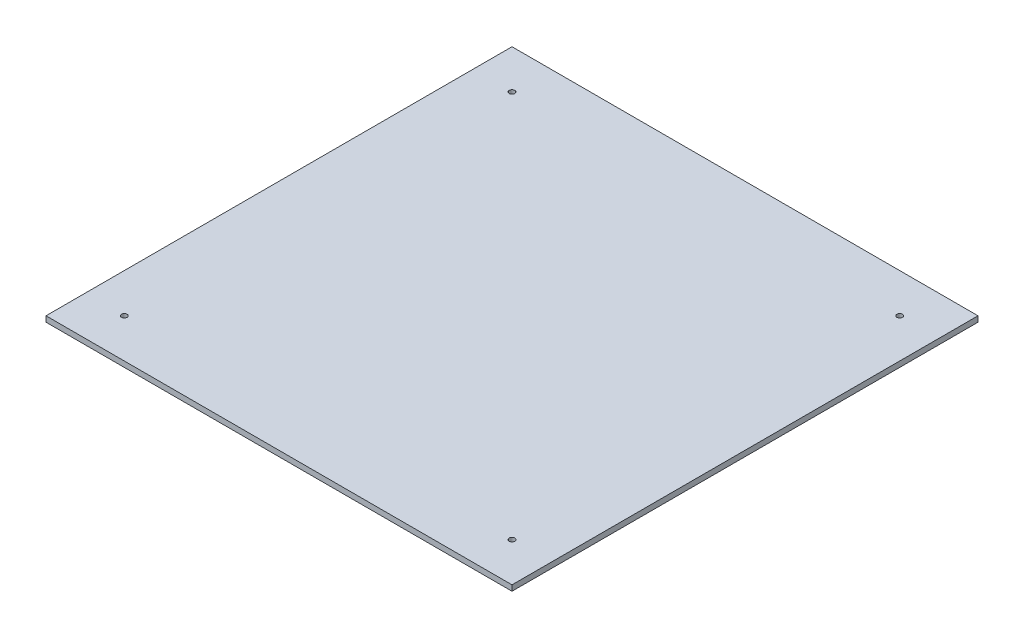
SolidWorks part; units mm, degrees
material "Balsa"
ref_plane "Plano frontal" through (0, 0, 0) normal (0, 0, 1) x (1, 0, 0)
ref_plane "Plano superior" through (0, 0, 0) normal (0, 1, 0) x (1, 0, 0)
ref_plane "Plano direito" through (0, 0, 0) normal (1, 0, 0) x (0, 0, -1)
sketch "Esboço1" plane through (0, 0, 0) normal (0, 1, 0) x (1, 0, 0)
  line L0 (-104, -104) -> (-104, 104) construction
  line L1 (-125, -125) -> (125, -125)
  line L2 (-125, -125) -> (-125, 125)
  line L3 (-125, 125) -> (125, 125)
  line L4 (125, -125) -> (125, 125)
  line L5 (-125, -125) -> (125, 125) construction
  line L6 (-125, 125) -> (125, -125) construction
  line L7 (0, 125) -> (0, -125) construction
  line L8 (104, -104) -> (104, 104) construction
  line L11 (-125, 0) -> (125, 0) construction
  circle A0 centre (-104, 104) radius 1.5
  circle A1 centre (-104, -104) radius 1.5
  circle A2 centre (104, -104) radius 1.5
  circle A3 centre (104, 104) radius 1.5
  point P0 (0, 0)
  point P12 (-104, 0)
  dimension "D4" = 3
  dimension "D1" = 250
  dimension "D2" = 250
  dimension "D3" = 208
extrude "Ressalto-extrusão1" add sketch "Esboço1" along normal blind 3
equation "\"D1@Esboço1\"=\"D2@Esboço1\""
